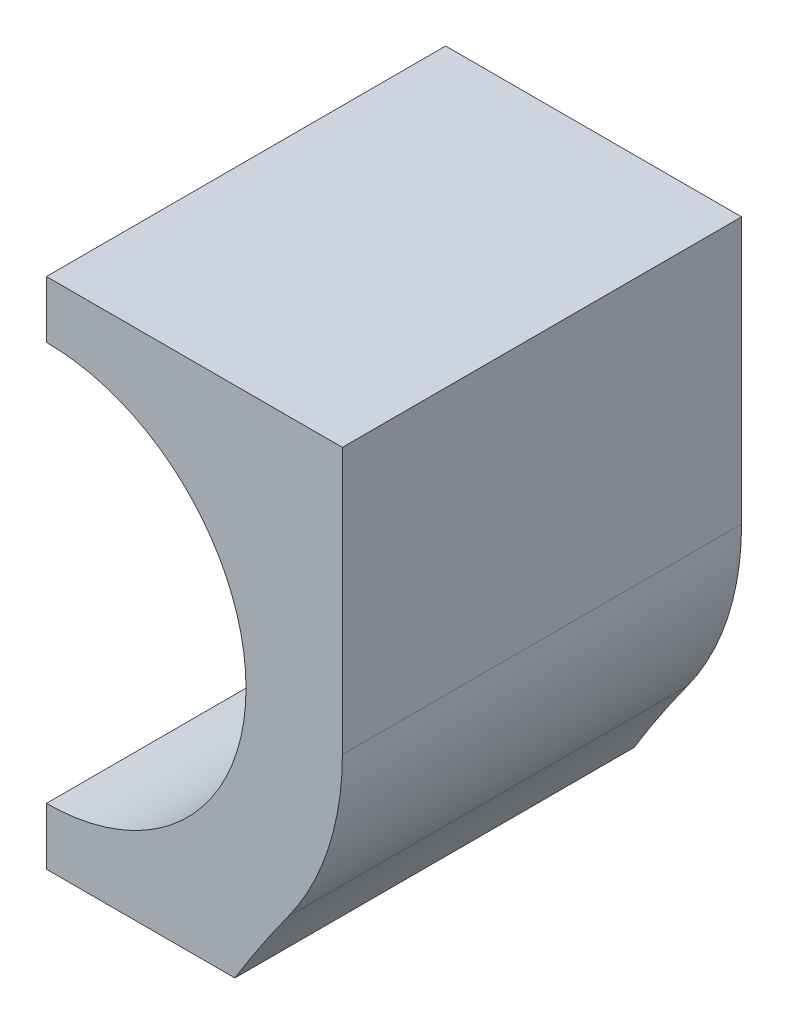
SolidWorks part; units mm, degrees
ref_plane "前视基准面" through (0, 0, 0) normal (0, 0, 1) x (1, 0, 0)
ref_plane "上视基准面" through (0, 0, 0) normal (0, 1, 0) x (1, 0, 0)
ref_plane "右视基准面" through (0, 0, 0) normal (1, 0, 0) x (0, 0, -1)
sketch "草图1" plane through (0, 0, 0) normal (0, 0, 1) x (1, 0, 0)
  line L1 (-4.3351, 439.9462) -> (-4.3351, 449.2768)
  line L2 (-14.713, 433.2768) -> (-14.713, 431.2768)
  line L3 (-14.713, 447.2768) -> (-14.713, 449.2768)
  line L4 (-14.713, 431.2768) -> (-8.105, 431.2768)
  line L5 (-14.713, 449.2768) -> (-4.3351, 449.2768)
  arc A3 (-6.2398, 434.0753) -> (-4.3351, 439.9462) centre (-14.3351, 439.9462) ccw
  arc A4 (-6.2398, 434.0753) -> (-8.105, 431.2768) centre (28.1649, 409.1241) ccw
  arc A5 (-14.713, 433.2768) -> (-14.713, 447.2768) centre (-14.713, 440.2768) ccw
extrude "凸台-拉伸1" add sketch "草图1" along normal up to surface (14 mm away)
